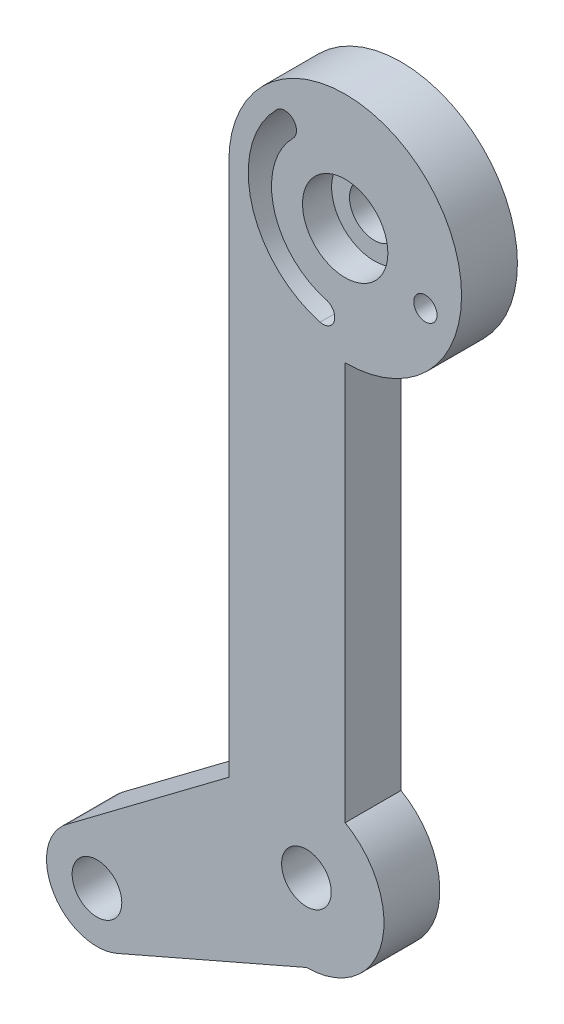
SolidWorks part; units mm, degrees
ref_plane "Front Plane" through (0, 0, 0) normal (0, 0, 1) x (1, 0, 0)
ref_plane "Top Plane" through (0, 0, 0) normal (0, 1, 0) x (1, 0, 0)
ref_plane "Right Plane" through (0, 0, 0) normal (1, 0, 0) x (0, 0, -1)
sketch "Sketch1" plane through (0, 0, 0) normal (0, 0, 1) x (1, 0, 0)
  line L0 (-5, 37.5) -> (-5, 3.1174)
  line L1 (2.5, 30) -> (2.5, 4.3301)
  line L2 (-12.2021, -10.3152) -> (0, -5)
  line L3 (-15.4525, -4.7374) -> (-5, 3.1174)
  line L4 (-13.5, -7.3356) -> (0, 0) construction
  line L5 (0, 0) -> (5, 0) construction
  circle A0 centre (0, 0) radius 1.6
  arc A1 (0, -5) -> (2.5, 4.3301) centre (0, 0) ccw
  circle A2 centre (-13.5, -7.3356) radius 1.6
  arc A3 (-15.4525, -4.7374) -> (-12.2021, -10.3152) centre (-13.5, -7.3356) ccw
  circle A4 centre (2.5, 37.5) radius 1.6
  arc A5 (2.5, 30) -> (-5, 37.5) centre (2.5, 37.5) ccw
  dimension "D1" = 3.2
  dimension "D4" = 5
  dimension "D5" = 3.25
  dimension "D6" = 7.5
  dimension "D7" = 12.2021
  dimension "D8" = 13.5
  dimension "D9" = 15.4525
  dimension "D10" = 30
extrude "Boss-Extrude1" add sketch "Sketch1" along normal blind 3.6
sketch "Sketch2" plane through (0, 0, 3.6) normal (0, 0, 1) x (1, 0, 0)
  line L0 (-5, 37.5) -> (-5, 3.1174) construction
  line L1 (2.5, 37.5) -> (-1.3891, 41.3891) construction
  line L2 (2.5, 37.5) -> (1.0765, 32.1874) construction
  line L3 (2.5, 37.5) -> (8, 37.5) construction
  line L4 (2.5, 37.5) -> (7.6683, 35.6189) construction
  circle A0 centre (7.6683, 35.6189) radius 0.75
  arc A1 (-0.8588, 40.8588) -> (-1.9194, 41.9194) centre (-1.3891, 41.3891) ccw
  arc A6 (0.8824, 31.463) -> (1.2706, 32.9119) centre (1.0765, 32.1874) ccw
  arc A7 (-1.9194, 41.9194) -> (0.8824, 31.463) centre (2.5, 37.5) ccw
  arc A8 (-0.8588, 40.8588) -> (1.2706, 32.9119) centre (2.5, 37.5) ccw
  dimension "D3" = 1.5
  dimension "D4" = 3.0806
  dimension "D2" = 120
  dimension "D1" = 6.25
  dimension "D5" = 20
extrude "Cut-Extrude1" cut sketch "Sketch2" against normal through all
sketch "Sketch3" [suppressed] plane through (0, 0, 0) normal (0, 0, -1) x (-1, 0, 0)
  circle A0 centre (-2.5, 30) radius 2.75
  dimension "D1" = 5.5
extrude "Cut-Extrude2" [suppressed] cut sketch "Sketch3" against normal blind 1.875
sketch "Sketch4" plane through (0, 0, 3.6) normal (0, 0, 1) x (1, 0, 0)
  circle A0 centre (2.5, 37.5) radius 2.75
  dimension "D1" = 5.5
extrude "Cut-Extrude3" cut sketch "Sketch4" against normal blind 1.875
sketch "Sketch5" plane through (0, 0, 3.6) normal (0, 0, 1) x (1, 0, 0)
  line L0 (0, 0) -> (-13.5, -7.3356) construction
sketch "Sketch6" [suppressed] plane through (0, 0, 3.6) normal (0, 0, 1) x (1, 0, 0)
  line L0 (0, 0) -> (-13.5, -7.3356) construction
sketch "Sketch7" plane through (0, 0, 3.6) normal (0, 0, 1) x (1, 0, 0)
  line L0 (2.5, 37.5) -> (0, 0) construction
  line L1 (0, 0) -> (1.0765, 32.1874) construction
